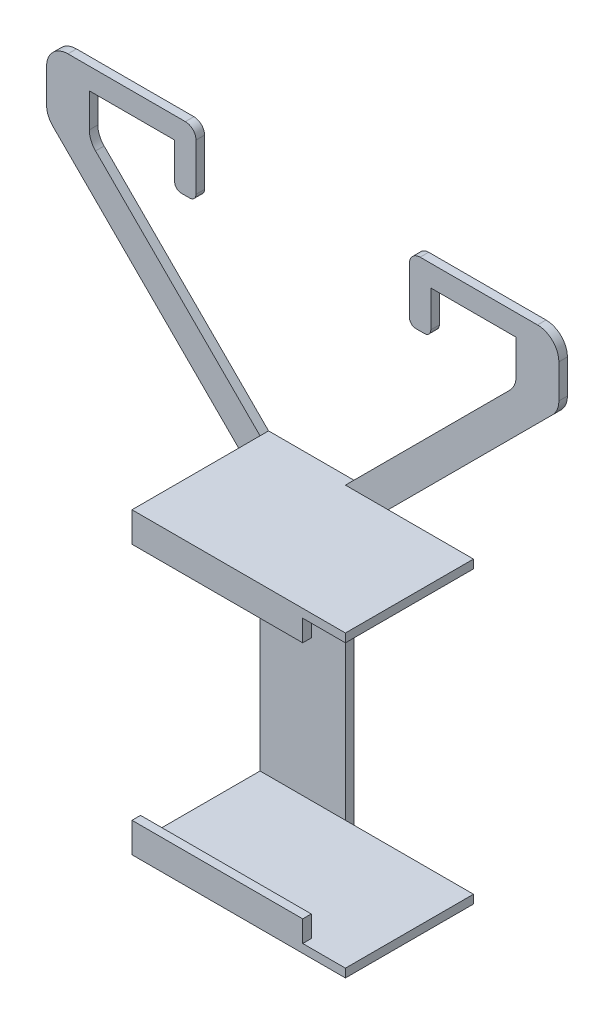
SolidWorks part; units mm, degrees
material "PVC 0.007 Plasticized"
ref_plane "Front Plane" through (0, 0, 0) normal (0, 0, 1) x (1, 0, 0)
ref_plane "Top Plane" through (0, 0, 0) normal (0, 1, 0) x (1, 0, 0)
ref_plane "Right Plane" through (0, 0, 0) normal (1, 0, 0) x (0, 0, -1)
sketch "base" plane through (0, 0, 0) normal (0, 0, 1) x (1, 0, 0)
  line L0 (-1000, 0) -> (49000, 0) construction
  line L1 (0, -1000) -> (0, 49000) construction
  line L2 (-10, 35) -> (10, 35)
  line L3 (-10, 35) -> (-10, -35)
  line L4 (-1004.969, -65) -> (48995.031, -65) construction
  line L5 (10, 35) -> (10, -35)
  line L13 (-10, 35) -> (-10, 25)
  line L14 (-990.1487, 65) -> (49009.8513, 65) construction
  line L19 (10, 35) -> (10.1268, 35.3102)
  line L23 (-10, -35) -> (10, -35)
  dimension "D1" = 70
  dimension "D3" = 20
  dimension "D4" = 20
  dimension "D12" = 70
sketch "hook" plane through (0, 0, 0) normal (0, 0, 1) x (1, 0, 0)
  line L0 (-10, 35) -> (-10, 25)
  line L1 (-40, -946.3832) -> (-40, 49053.6168) construction
  line L2 (0, -201000) -> (0, 249000) construction
  line L3 (-10, 25) -> (-58.5355, 73.5355)
  line L4 (-60, 77.0711) -> (-60, 85)
  line L5 (-55, 90) -> (-27.5, 90)
  line L6 (-25, 87.5) -> (-25, 76.5)
  line L7 (-26.5, 75) -> (-28.5, 75)
  line L8 (-30, 76.5) -> (-30, 85)
  line L9 (-30, 85) -> (-50, 85)
  line L10 (-50, 85) -> (-50, 77.0711)
  line L11 (-48.5355, 73.5355) -> (-10, 35)
  line L12 (-10, 35) -> (10, 35) construction
  line L13 (0, -1000) -> (0, 49000) construction
  line L14 (48.5355, 73.5355) -> (10, 35)
  line L15 (50, 85) -> (50, 77.0711)
  line L16 (30, 85) -> (50, 85)
  line L17 (30, 76.5) -> (30, 85)
  line L18 (26.5, 75) -> (28.5, 75)
  line L19 (25, 87.5) -> (25, 76.5)
  line L20 (55, 90) -> (27.5, 90)
  line L21 (60, 77.0711) -> (60, 85)
  line L22 (10, 25) -> (58.5355, 73.5355)
  line L23 (10, 35) -> (10, 25)
  arc A0 (-60, 85) -> (-55, 90) centre (-55, 85) cw
  arc A1 (-50, 77.0711) -> (-48.5355, 73.5355) centre (-45, 77.0711) ccw
  arc A2 (-58.5355, 73.5355) -> (-60, 77.0711) centre (-55, 77.0711) cw
  arc A3 (-27.5, 90) -> (-25, 87.5) centre (-27.5, 87.5) cw
  arc A4 (-25, 76.5) -> (-26.5, 75) centre (-26.5, 76.5) cw
  arc A5 (-28.5, 75) -> (-30, 76.5) centre (-28.5, 76.5) cw
  arc A6 (28.5, 75) -> (30, 76.5) centre (28.5, 76.5) ccw
  arc A7 (25, 76.5) -> (26.5, 75) centre (26.5, 76.5) ccw
  arc A8 (27.5, 90) -> (25, 87.5) centre (27.5, 87.5) ccw
  arc A9 (58.5355, 73.5355) -> (60, 77.0711) centre (55, 77.0711) ccw
  arc A10 (50, 77.0711) -> (48.5355, 73.5355) centre (45, 77.0711) cw
  arc A11 (60, 85) -> (55, 90) centre (55, 85) ccw
  point P23 (-50, 75)
  point P26 (-60, 75)
  point P31 (-25, 75)
  point P34 (-30, 75)
  point P59 (30, 75)
  point P60 (25, 75)
  point P61 (60, 75)
  point P62 (50, 75)
  dimension "D8" = 5
  dimension "D9" = 2.5
  dimension "D10" = 1.5
  dimension "D1" = 40
  dimension "D2" = 20
  dimension "D3" = 20
  dimension "D4" = 5
  dimension "D5" = 45
  dimension "D6" = 10
  dimension "D7" = 5
extrude "Boss-Extrude1" add sketch "hook" against normal blind 2
extrude "Boss-Extrude2" add sketch "base" against normal blind 2 contours L3 L23 L5 L2
ref_plane "upper Plane" through (0, 35, 0) normal (0, 1, 0) x (1, 0, 0)
ref_plane "lower Plane" through (0, -35, 0) normal (0, 1, 0) x (1, 0, 0)
sketch "Sketch9" plane through (0, 35, 0) normal (0, 1, 0) x (1, 0, 0)
  line L0 (-10, 0) -> (40, 0)
  line L1 (40, 0) -> (40, -30)
  line L2 (-10, -30) -> (40, -30)
  line L3 (-10, -30) -> (-10, 0)
  dimension "D1" = 30
  dimension "D2" = 50
sketch "Sketch10" plane through (0, -35, 0) normal (0, 1, 0) x (1, 0, 0)
  line L0 (-10, 0) -> (40, 0)
  line L1 (48.5355, 0) -> (10, 0) construction
  line L2 (40, 0) -> (40, -30)
  line L3 (40, -30) -> (-10, -30)
  line L6 (-10, -30) -> (-10, 0)
  dimension "D1" = 50
  dimension "D2" = 30
extrude "Boss-Extrude3" add sketch "Sketch10" along normal blind 2 separate body
extrude "Boss-Extrude4" add sketch "Sketch9" against normal blind 2
ref_plane "holding plane" through (0, 0, 30) normal (0, 0, 1) x (1, 0, 0)
sketch "Sketch11" plane through (0, 0, 30) normal (0, 0, 1) x (1, 0, 0)
  line L0 (-10, -33) -> (30, -33)
  line L1 (-10, -33) -> (40, -33) construction
  line L2 (30, -33) -> (30, -28)
  line L3 (30, -28) -> (-10, -28)
  line L4 (-10, -28) -> (-10, -33)
  line L5 (-10, 33) -> (-10, 28)
  line L6 (-10, 28) -> (30, 28)
  line L7 (30, 28) -> (30, 33)
  line L8 (-10, 33) -> (40, 33) construction
  line L9 (30, 33) -> (-10, 33)
  dimension "D1" = 5
  dimension "D2" = 40
  dimension "D3" = 5
  dimension "D4" = 40
extrude "Boss-Extrude5" add sketch "Sketch11" against normal blind 2
